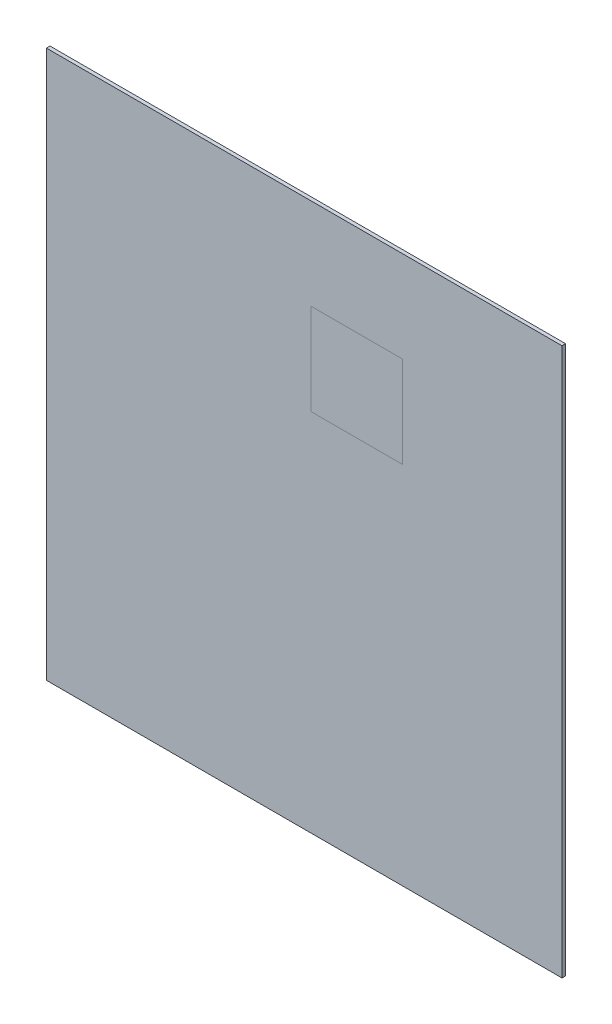
SolidWorks part; units mm, degrees
ref_plane "Front Plane" through (0, 0, 0) normal (0, 0, 1) x (1, 0, 0)
ref_plane "Top Plane" through (0, 0, 0) normal (0, 1, 0) x (1, 0, 0)
ref_plane "Right Plane" through (0, 0, 0) normal (1, 0, 0) x (0, 0, -1)
sketch "Sketch1" plane through (0, 0, 0) normal (0, 0, 1) x (1, 0, 0)
  line L1 (-113, -120) -> (113, -120)
  line L2 (-113, -120) -> (-113, 120)
  line L3 (-113, 120) -> (113, 120)
  line L4 (113, -120) -> (113, 120)
  line L5 (-113, -120) -> (113, 120) construction
  line L6 (-113, 120) -> (113, -120) construction
  point P0 (0, 0)
  dimension "D1" = 226
  dimension "D2" = 240
extrude "Boss-Extrude1" add sketch "Sketch1" along normal blind 1.57
sketch "Sketch2" plane through (0, 0, 1.57) normal (0, 0, 1) x (1, 0, 0)
  line L0 (113, 120) -> (-113, 120) construction
  line L1 (3, 40) -> (43, 40)
  line L2 (3, 40) -> (3, 80)
  line L3 (3, 80) -> (43, 80)
  line L4 (43, 40) -> (43, 80)
  line L5 (3, 40) -> (43, 80) construction
  line L6 (3, 80) -> (43, 40) construction
  line L7 (113, -120) -> (113, 120) construction
  point P0 (23, 60)
  point P9 (0, 36.8355)
  dimension "D1" = 40
  dimension "D2" = 70
  dimension "D3" = 40
split "Split1" trim tools "Sketch2" bodies to split 101 resulting bodies 102 103
